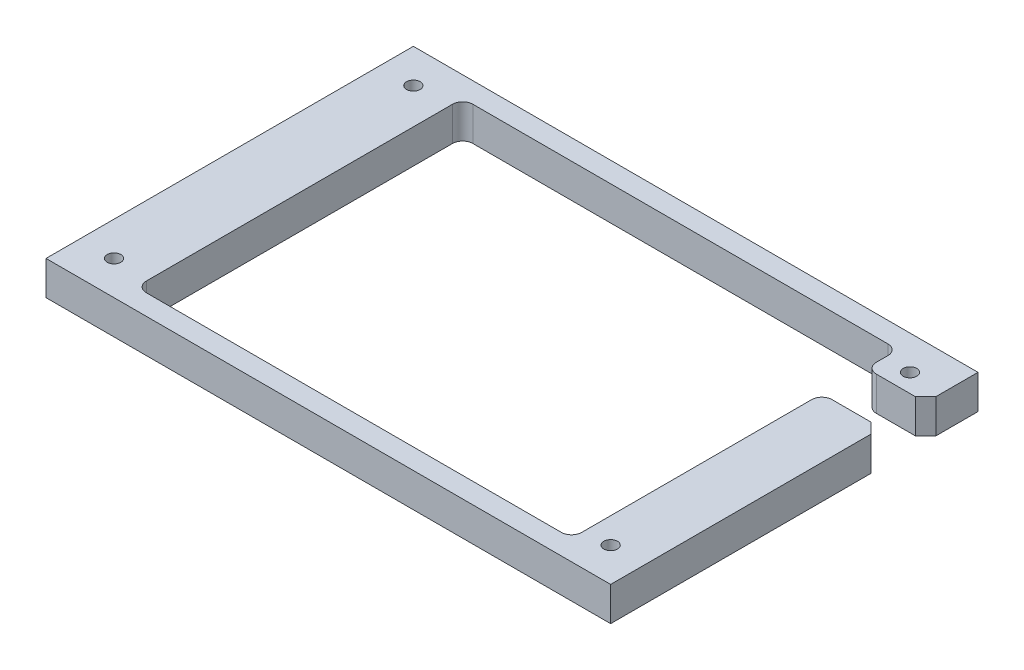
SolidWorks part; units mm, degrees
material "Стекло кварцевое прозрачное"
ref_plane "Спереди" through (0, 0, 0) normal (0, 0, 1) x (1, 0, 0)
ref_plane "Сверху" through (0, 0, 0) normal (0, 1, 0) x (1, 0, 0)
ref_plane "Справа" through (0, 0, 0) normal (1, 0, 0) x (0, 0, -1)
sketch "Эскиз1" plane through (0, 0, 0) normal (0, 1, 0) x (1, 0, 0)
  line L1 (-83, -54) -> (83, -54)
  line L2 (-83, -54) -> (-83, 54)
  line L3 (-83, 54) -> (83, 54)
  line L4 (83, -54) -> (83, 54)
  line L5 (-83, -54) -> (83, 54) construction
  line L6 (-83, 54) -> (83, -54) construction
  point P0 (0, 0)
  dimension "D1" = 166
  dimension "D2" = 108
extrude "Бобышка-Вытянуть1" add sketch "Эскиз1" along normal blind 10
sketch "Эскиз2" plane through (0, 10, 0) normal (0, 1, 0) x (1, 0, 0)
  circle A0 centre (-73, 44) radius 2
  circle A1 centre (73, 44) radius 2
  circle A2 centre (-73, -44) radius 2
  circle A3 centre (73, -44) radius 2
  dimension "D2" = 44
  dimension "D4" = 4
  dimension "D8" = 44
  dimension "D9" = 73
  dimension "D10" = 73
extrude "Крепежные отверстия" cut sketch "Эскиз2" against normal through all
sketch "Эскиз4" plane through (0, 10, 0) normal (0, 1, 0) x (1, 0, 0)
  line L0 (-83, 54) -> (-83, -54) construction
  line L1 (-62.5, -48) -> (65.5, -48)
  line L2 (-62.5, -48) -> (-62.5, 48)
  line L3 (-62.5, 48) -> (65.5, 48)
  line L4 (65.5, -48) -> (65.5, 48)
  line L5 (-62.5, -48) -> (65.5, 48) construction
  line L6 (-62.5, 48) -> (65.5, -48) construction
  line L7 (83, -54) -> (83, 54) construction
  line L8 (83, 54) -> (-83, 54) construction
  line L9 (-83, -54) -> (83, -54) construction
  point P0 (0, 0)
  dimension "D1" = 20.5
  dimension "D2" = 17.5
  dimension "D3" = 6
  dimension "D4" = 6
extrude "Центральный вырез" cut sketch "Эскиз4" against normal through all
sketch "Эскиз5" plane through (0, 10, 0) normal (0, 1, 0) x (1, 0, 0)
  line L0 (83, 54) -> (-83, 54) construction
  line L1 (65.5, 38.6) -> (83, 38.6)
  line L2 (65.5, 38.6) -> (65.5, 25.6)
  line L3 (65.5, 25.6) -> (83, 25.6)
  line L4 (83, 38.6) -> (83, 25.6)
  line L5 (74.25, 38.6) -> (74.25, 25.6) construction
  line L6 (65.5, -48) -> (65.5, 48) construction
  line L7 (83, -54) -> (83, 54) construction
  point P5 (65.5, 32.1)
  point P8 (74.25, 32.1)
  dimension "D1" = 13
  dimension "D2" = 21.9
extrude " Под usb" cut sketch "Эскиз5" against normal through all
fillet "Скругление1" radius 3 4 edges at (65.5, 5, -48) (65.5, 5, 48) (-62.5, 5, 48) (-62.5, 5, -48)
chamfer "Фаска1" distance 3 angle 45 2 edges at (83, 5, -25.6) (83, 5, -38.6)
fillet "Скругление2" radius 3 2 edges at (65.5, 5, -25.6) (65.5, 5, -38.6)
